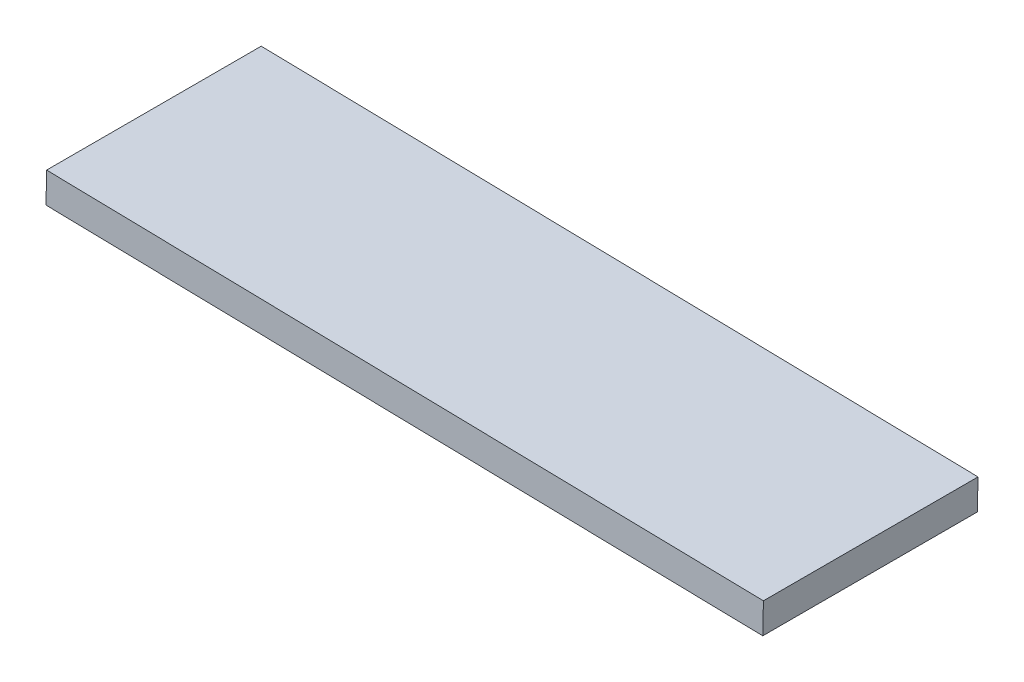
SolidWorks part; units mm, degrees
ref_plane "Front Plane" through (0, 0, 0) normal (0, 0, 1) x (1, 0, 0)
ref_plane "Top Plane" through (0, 0, 0) normal (0, 1, 0) x (1, 0, 0)
ref_plane "Right Plane" through (0, 0, 0) normal (1, 0, 0) x (0, 0, -1)
sketch "Sketch4" plane through (11.9471, 45.5502, 0) normal (0, 0, 1) x (0.9673, -0.2537, 0)
  line L6 (-78.1169, 415.2878) -> (-191.804, 387.9379)
  line L7 (-78.1169, 415.2878) -> (-79.2864, 420.1491)
  line L8 (-191.804, 387.9379) -> (-192.9735, 392.7992)
  line L9 (-79.2864, 420.1491) -> (-192.9735, 392.7992)
  line L10 (-191.5567, 387.9974) -> (-81.9458, 414.3667) construction
  line L13 (-66.6786, 395.4868) -> (-79.1783, 419.9375) construction
  point P7 (0, 0)
  dimension "D1" = 5
extrude "Boss-Extrude1" add sketch "Sketch4" along normal blind 35
